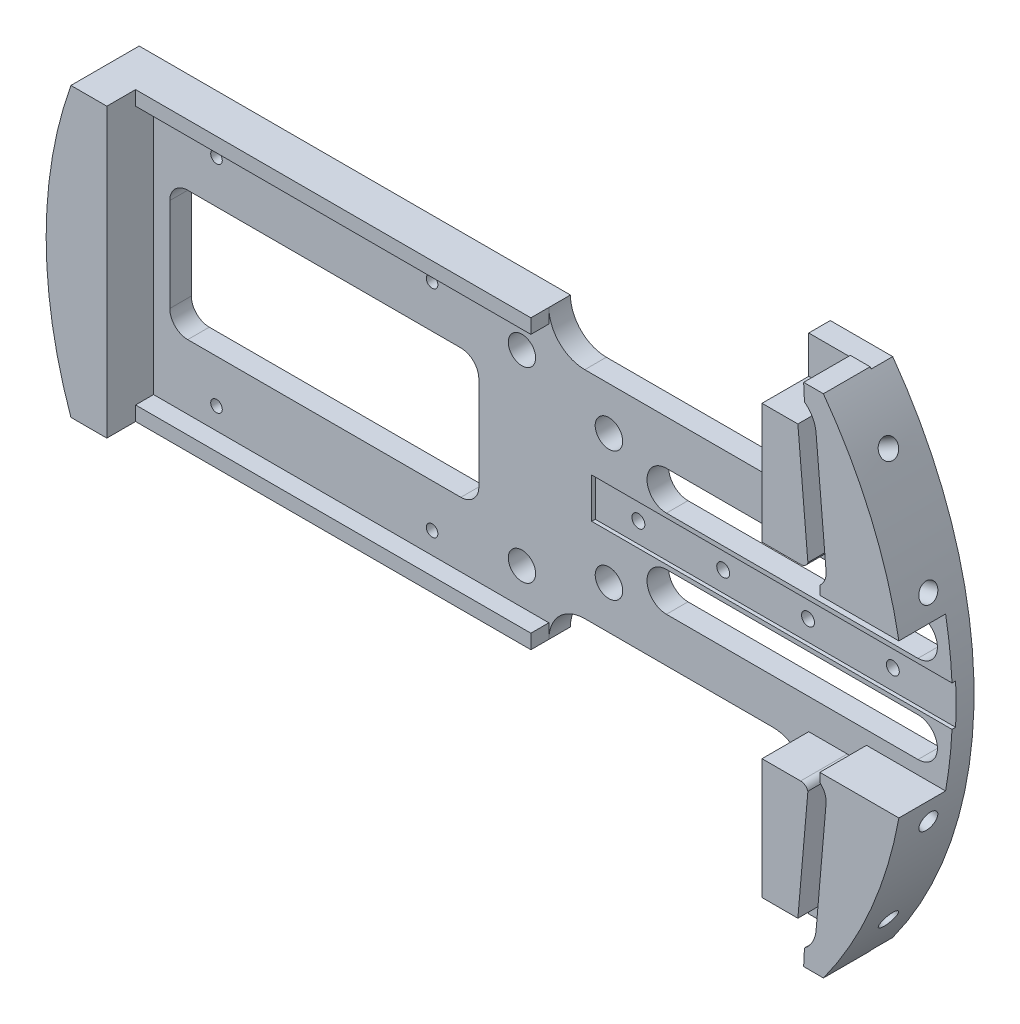
SolidWorks part; units mm, degrees
ref_plane "Front Plane" through (0, 0, 0) normal (0, 0, 1) x (1, 0, 0)
ref_plane "Top Plane" through (0, 0, 0) normal (0, 1, 0) x (1, 0, 0)
ref_plane "Right Plane" through (0, 0, 0) normal (1, 0, 0) x (0, 0, -1)
sketch "Sketch1" plane through (0, 0, 0) normal (0, 0, 1) x (1, 0, 0)
  line L0 (0, 0) -> (91.8237, 0) construction
  line L1 (10.9774, 19.05) -> (44.196, 19.05)
  line L2 (-71.5726, 25.4) -> (4.6274, 25.4)
  line L3 (10.9774, -19.05) -> (44.196, -19.05)
  line L6 (50.546, 44.45) -> (61.5792, 44.45)
  line L7 (50.546, -44.45) -> (61.5792, -44.45)
  line L11 (-71.5726, -25.4) -> (4.6274, -25.4)
  line L12 (50.546, 25.4) -> (50.546, 44.45)
  line L14 (50.546, -25.4) -> (50.546, -44.45)
  arc A0 (61.5792, -44.45) -> (61.5792, 44.45) centre (0, 0) ccw
  circle A1 centre (0, 0) radius 75.946 construction
  arc A2 (-71.5726, 25.4) -> (-71.5726, -25.4) centre (0, 0) ccw
  arc A3 (44.196, 19.05) -> (50.546, 25.4) centre (44.196, 25.4) ccw
  arc A4 (10.9774, 19.05) -> (4.6274, 25.4) centre (10.9774, 25.4) cw
  arc A5 (44.196, -19.05) -> (50.546, -25.4) centre (44.196, -25.4) cw
  arc A6 (10.9774, -19.05) -> (4.6274, -25.4) centre (10.9774, -25.4) ccw
  point P6 (75.946, 0)
  point P17 (0, 0)
  dimension "D1" = 75.946
  dimension "D8" = 151.892
  dimension "D11" = 75.946
  dimension "D2" = 76.2
  dimension "D3" = 6.35
  dimension "D4" = 25.4
  dimension "D5" = 50.8
  dimension "D6" = 88.9
  dimension "D7" = 6.35
  dimension "D9" = 6.35
  dimension "D10" = 6.35
extrude "Boss-Extrude1" add sketch "Sketch1" along normal blind 3.81
sketch "Sketch2" plane through (0, 0, 3.81) normal (0, 0, 1) x (1, 0, 0)
  line L0 (60.2463, 17.78) -> (56.2059, 64.1603) construction
  line L1 (-13.9228, 0) -> (116.9939, 0) construction
  line L2 (35.7924, 17.78) -> (109.7023, 17.78) construction
  line L3 (61.8653, 17.78) -> (60.0951, 38.1)
  line L4 (58.6516, 17.5) -> (56.8815, 37.82)
  line L5 (56.8815, 37.82) -> (50.546, 37.82)
  line L6 (58.0471, 41.7789) -> (57.9008, 44.704)
  line L7 (57.9008, 44.704) -> (61.395, 44.704)
  line L8 (50.546, 37.82) -> (50.546, 16.5667)
  line L9 (50.546, 16.5667) -> (57.3661, 16.5667)
  line L10 (60.7595, 15.0941) -> (60.7595, 13.5449)
  line L11 (60.7595, 13.5449) -> (74.7284, 13.5449)
  line L12 (60.2463, -17.78) -> (56.2059, -64.1603) construction
  line L13 (60.7595, -13.5449) -> (74.7284, -13.5449)
  line L14 (60.7595, -15.0941) -> (60.7595, -13.5449)
  line L15 (50.546, -16.5667) -> (57.3661, -16.5667)
  line L16 (50.546, -37.82) -> (50.546, -16.5667)
  line L17 (57.9008, -44.704) -> (61.395, -44.704)
  line L18 (58.0471, -41.7789) -> (57.9008, -44.704)
  line L19 (56.8815, -37.82) -> (50.546, -37.82)
  line L20 (58.6516, -17.5) -> (56.8815, -37.82)
  line L21 (61.8653, -17.78) -> (60.0951, -38.1)
  line L22 (96.3863, 0) -> (96.3863, 82.276) construction
  arc A0 (61.5792, -44.45) -> (61.5792, 44.45) centre (0, 0) ccw construction
  arc A1 (60.0951, 38.1) -> (58.0471, 41.7789) centre (54.9639, 37.653) ccw
  arc A2 (57.3661, 16.5667) -> (58.6516, 17.5) centre (57.3661, 17.9187) ccw
  arc A3 (61.8653, 17.78) -> (60.7595, 15.0941) centre (58.7167, 17.5057) cw
  arc A4 (74.7284, 13.5449) -> (61.395, 44.704) centre (0, 0) ccw
  arc A5 (74.7284, -13.5449) -> (61.395, -44.704) centre (0, 0) cw
  arc A6 (61.8653, -17.78) -> (60.7595, -15.0941) centre (58.7167, -17.5057) ccw
  arc A7 (57.3661, -16.5667) -> (58.6516, -17.5) centre (57.3661, -17.9187) cw
  arc A8 (60.0951, -38.1) -> (58.0471, -41.7789) centre (54.9639, -37.653) cw
  point P0 (75.946, 0)
  point P1 (60.2463, 17.78)
  point P49 (96.3863, 44.704)
  dimension "D6" = 75.946
  dimension "D1" = 17.78
  dimension "D2" = 15.6997
  dimension "D3" = 85.021
  dimension "D4" = 1.6129
  dimension "D5" = 20.32
  dimension "D7" = 44.704
  dimension "D8" = 44.704
  dimension "D9" = 25.4
extrude "Boss-Extrude2" add sketch "Sketch2" along normal blind 8.255
sketch "Sketch3" plane through (0, 0, 3.81) normal (0, 0, 1) x (1, 0, 0)
  line L0 (-6.3906, 0) -> (92.2963, 0) construction
  line L2 (12.192, -3.55) -> (76.962, -3.55)
  line L3 (12.192, -3.55) -> (12.192, 3.55)
  line L4 (12.192, 3.55) -> (76.962, 3.55)
  line L5 (76.962, -3.55) -> (76.962, 3.55)
  line L6 (12.192, -3.55) -> (76.962, 3.55) construction
  line L7 (12.192, 3.55) -> (76.962, -3.55) construction
  line L8 (50.546, 16.5667) -> (50.546, 25.4) construction
  point P3 (44.577, 0)
  dimension "D1" = 7.1
  dimension "D2" = 64.77
  dimension "D3" = 38.354
extrude "Cut-Extrude1" cut sketch "Sketch3" against normal blind 0.635
sketch "Sketch6" plane through (0, 0, 0) normal (0, 0, -1) x (-1, 0, 0)
  line L1 (102.4877, 0) -> (-122.8054, 0) construction
sketch "Sketch7" plane through (0, 0, 0) normal (0, 0, 1) x (1, 0, 0)
  line L0 (0, 0) -> (107.1474, 0) construction
  line L1 (0, 0) -> (65.9911, 38.1) construction
  dimension "D1" = 30
ref_plane "Plane2" through (65.7712, 37.973, 0) normal (0.866, 0.5, 0) x (0, 0, -1)
sketch "Sketch9" plane through (0, 0, 3.81) normal (0, 0, 1) x (1, 0, 0)
  line L0 (-35.0108, 0) -> (91.9546, 0) construction
  line L1 (75.863, 3.55) -> (12.192, 3.55) construction
  line L2 (69.85, 11.17) -> (25.4, 11.17)
  line L3 (69.85, 11.17) -> (69.85, 4.312) construction
  line L4 (69.85, 4.312) -> (25.4, 4.312)
  line L5 (25.4, 11.17) -> (25.4, 4.312) construction
  line L6 (69.85, -4.312) -> (25.4, -4.312)
  line L7 (69.85, -11.17) -> (25.4, -11.17)
  arc A0 (25.4, 11.17) -> (25.4, 4.312) centre (25.4, 7.741) ccw
  arc A1 (69.85, 11.17) -> (69.85, 4.312) centre (69.85, 7.741) cw
  arc A2 (69.85, -11.17) -> (69.85, -4.312) centre (69.85, -7.741) ccw
  arc A3 (25.4, -11.17) -> (25.4, -4.312) centre (25.4, -7.741) cw
  point P9 (74.93, 0)
  dimension "D1" = 6.858
  dimension "D2" = 0.762
  dimension "D3" = 44.45
  dimension "D4" = 74.93
  dimension "D5" = 5.08
extrude "Cut-Extrude4" cut sketch "Sketch9" against normal through all
sketch "Sketch10" plane through (0, 0, 3.81) normal (0, 0, 1) x (1, 0, 0)
  line L0 (50.546, 37.82) -> (50.546, 16.5667) construction
  line L1 (-5.2199, 8.255) -> (-40.7011, 8.255) construction
  line L2 (-35.052, -6.0075) -> (-35.052, 31.8531) construction
  line L3 (-10.922, 11.43) -> (-59.182, 11.43)
  line L4 (-7.747, -8.255) -> (-7.747, 8.255)
  line L5 (-82.1806, 0) -> (28.287, 0) construction
  line L6 (-62.357, -8.255) -> (-62.357, 8.255)
  line L7 (-10.922, -11.43) -> (-59.182, -11.43)
  line L8 (-102.4877, 0) -> (122.8054, 0) construction
  arc A0 (-7.747, 8.255) -> (-10.922, 11.43) centre (-10.922, 8.255) ccw
  arc A1 (-62.357, 8.255) -> (-59.182, 11.43) centre (-59.182, 8.255) cw
  arc A2 (-7.747, -8.255) -> (-10.922, -11.43) centre (-10.922, -8.255) cw
  arc A3 (-62.357, -8.255) -> (-59.182, -11.43) centre (-59.182, -8.255) ccw
  point P0 (-35.052, 0)
  point P16 (-35.052, 15.5292)
  point P19 (-4.5185, 0)
  point P22 (-35.052, 11.43)
  point P24 (-65.5855, 0)
  dimension "D1" = 16.51
  dimension "D2" = 3.175
  dimension "D3" = 48.26
  dimension "D4" = 58.293
  dimension "D5" = 3.175
  dimension "D6" = 3.175
extrude "Cut-Extrude5" cut sketch "Sketch10" against normal through all
sketch "Sketch12" plane through (0, 0, 3.81) normal (0, 0, 1) x (1, 0, 0)
  line L0 (15.24, 51.8718) -> (15.24, -46.8025) construction
  line L1 (50.546, 37.82) -> (50.546, 16.5667) construction
  line L2 (0, 0) -> (87.8985, 0) construction
  line L3 (-102.4877, 0) -> (122.8054, 0) construction
  circle A0 centre (15.24, 11.43) radius 2.4257
  circle A1 centre (15.24, -11.43) radius 2.4257
  dimension "D2" = 4.8514
  dimension "D1" = 35.306
  dimension "D3" = 11.43
extrude "Cut-Extrude6" cut sketch "Sketch12" against normal through all
sketch "Sketch4" plane through (0, 0, 3.175) normal (0, 0, 1) x (1, 0, 0)
  line L0 (12.192, 3.55) -> (12.192, -3.55) construction
  line L1 (-1.4827, 0) -> (103.4049, 0) construction
  circle A0 centre (19.812, 0) radius 1.143
  circle A1 centre (34.798, 0) radius 1.143
  circle A2 centre (49.784, 0) radius 1.143
  circle A3 centre (64.77, 0) radius 1.143
  point P2 (12.192, 0)
  dimension "D2" = 2.286
  dimension "D4" = 14.986
  dimension "D1" = 7.62
  dimension "D5" = 19.812
  dimension "D3" = 4
extrude "Cut-Extrude2" cut sketch "Sketch4" against normal blind 11.43
sketch "Sketch17" plane through (0, 0, 3.81) normal (0, 0, 1) x (1, 0, 0)
  line L0 (-87.521, 0) -> (99.4626, 0) construction
  line L1 (-102.4877, 0) -> (122.8054, 0) construction
  line L3 (-0.127, 0) -> (-0.127, 33.8266) construction
  line L5 (-7.747, -8.255) -> (-7.747, 8.255) construction
  circle A0 centre (-0.127, 16.51) radius 2.413
  circle A2 centre (-0.127, -16.51) radius 2.413
  dimension "D1" = 4.826
  dimension "D2" = 16.51
  dimension "D3" = 7.62
extrude "Cut-Extrude9" cut sketch "Sketch17" against normal through all
sketch "Sketch19" plane through (0, 0, 3.81) normal (0, 0, 1) x (1, 0, 0)
  line L0 (-71.5726, -25.4) -> (4.6274, -25.4) construction
  line L3 (-71.5726, -25.4) -> (-65.2226, -25.4)
  line L4 (-65.2226, -25.4) -> (-65.2226, 25.4)
  line L5 (4.6274, 25.4) -> (-71.5726, 25.4) construction
  line L6 (-65.2226, 25.4) -> (-71.5726, 25.4)
  circle A0 centre (0, 0) radius 75.946 construction
  arc A3 (-71.5726, 25.4) -> (-71.5726, -25.4) centre (0, 0) ccw
  point P0 (-65.2226, -25.4)
  point P6 (-71.5726, -25.4)
  dimension "D2" = 151.892
  dimension "D1" = 6.35
extrude "Boss-Extrude5" add sketch "Sketch19" along normal blind 8.255
sketch "Sketch20" plane through (0, -25.4, 0) normal (0, -1, 0) x (1, 0, 0)
  line L0 (-65.2226, 3.81) -> (4.6274, 3.81)
  line L1 (4.6274, 3.81) -> (4.6274, 6.985)
  line L2 (4.6274, 6.985) -> (-65.2226, 6.985)
  line L3 (-65.2226, 12.065) -> (-65.2226, 3.81) construction
  line L4 (-65.2226, 6.985) -> (-65.2226, 3.81)
  dimension "D1" = 3.175
extrude "Boss-Extrude6" add sketch "Sketch20" against normal blind 2.54
mirror "Mirror1" about plane through (0, 0, 0) normal (0, 1, 0) of "Boss-Extrude6"
sketch "Sketch21" plane through (0, 0, 0) normal (0, 0, -1) x (-1, 0, 0)
  line L1 (16.002, -19.05) -> (54.102, -19.05) construction
  line L2 (16.002, -19.05) -> (16.002, 19.05) construction
  line L3 (16.002, 19.05) -> (54.102, 19.05) construction
  line L4 (54.102, -19.05) -> (54.102, 19.05) construction
  line L5 (16.002, -19.05) -> (54.102, 19.05) construction
  line L6 (16.002, 19.05) -> (54.102, -19.05) construction
  line L12 (35.052, 11.43) -> (35.052, -11.43) construction
  line L13 (10.922, 11.43) -> (59.182, 11.43) construction
  line L14 (59.182, -11.43) -> (10.922, -11.43) construction
  circle A0 centre (54.102, 19.05) radius 1.0224
  circle A1 centre (16.002, 19.05) radius 1.0223
  circle A2 centre (16.002, -19.05) radius 1.0223
  circle A3 centre (54.102, -19.05) radius 1.0224
  point P14 (35.052, 0)
  point P15 (35.052, 0)
  point P16 (35.052, 0)
  dimension "D3" = 2.0447
  dimension "D5" = 2.0447
  dimension "D6" = 2.0447
  dimension "D7" = 2.0447
  dimension "D1" = 38.1
  dimension "D2" = 38.1
extrude "Cut-Extrude10" cut sketch "Sketch21" against normal through all
ref_plane "Plane3" through (0, 0, 12.065) normal (0, 0, 1) x (1, 0, 0)
sketch "Sketch22" plane through (0, 0, 12.065) normal (0, 0, 1) x (1, 0, 0)
  line L1 (-75.946, -44.45) -> (75.946, -44.45) construction
  line L2 (-75.946, -44.45) -> (-75.946, 44.45) construction
  line L3 (-75.946, 44.45) -> (75.946, 44.45) construction
  line L4 (75.946, -44.45) -> (75.946, 44.45) construction
  line L5 (-75.946, -44.45) -> (75.946, 44.45) construction
  line L6 (-75.946, 44.45) -> (75.946, -44.45) construction
  point P0 (0, 0)
  dimension "D1" = 88.9
  dimension "D2" = 151.892
sketch "Sketch24" plane through (65.7712, 37.973, 0) normal (0.866, 0.5, 0) x (0, 0, -1)
  line L0 (0, -69.2844) -> (0, 7.7053) construction
  circle A0 centre (-6.0325, -2.2244) radius 1.6383
  dimension "D1" = 3.2766
  dimension "D2" = 6.0325
extrude "Cut-Extrude11" cut sketch "Sketch24" against normal blind 8.128
pattern_circular "CirPattern1" count 2 over 15 about axis through (0, 0, 3.81) along (0, 0, -1) of "Cut-Extrude11"
mirror "Mirror2" about plane through (0, 0, 0) normal (0, 1, 0) of "CirPattern1", "Cut-Extrude11"
equation "\"0.15inin\"=0.2"
equation "\"0.45inin\"=0.35"
equation "\"0.55inin\"=0.45"
equation "\"0.125inin\"=0.325"
